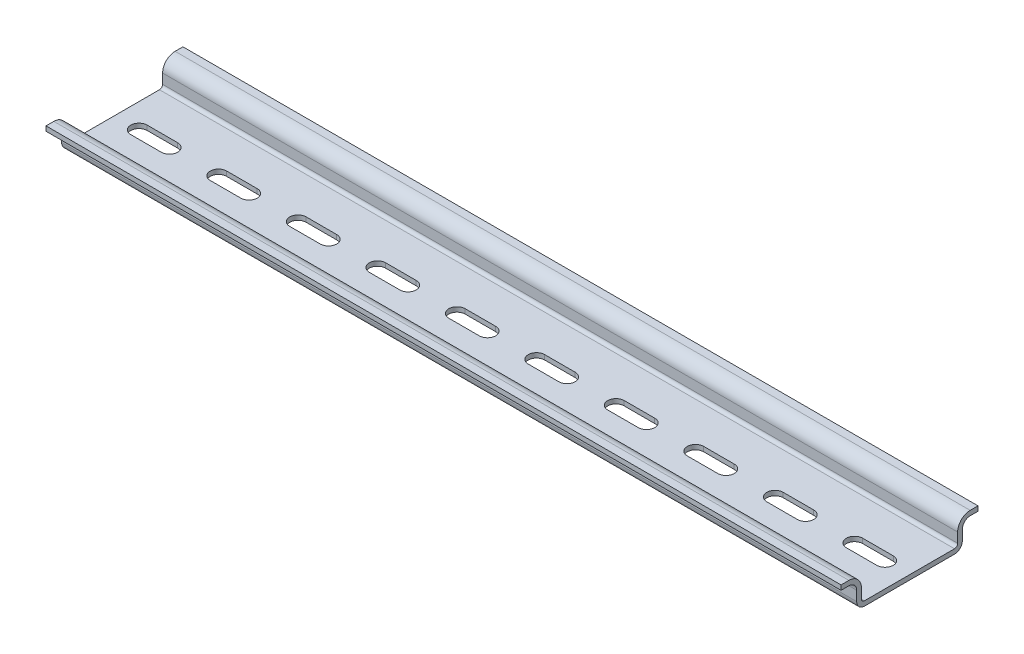
SolidWorks part; units mm, degrees
material "1060 Alloy"
ref_plane "Front Plane" through (0, 0, 0) normal (0, 0, 1) x (1, 0, 0)
ref_plane "Top Plane" through (0, 0, 0) normal (0, 1, 0) x (1, 0, 0)
ref_plane "Right Plane" through (0, 0, 0) normal (1, 0, 0) x (0, 0, -1)
sketch "Sketch1" plane through (0, 0, 0) normal (1, 0, 0) x (0, 0, -1)
  line L0 (0, 0) -> (0, 6.5) construction
  line L1 (0, 0) -> (17.5, 0) construction
  line L2 (-11.5, 0) -> (11.5, 0)
  line L3 (13.5, 2) -> (13.5, 4.5)
  line L4 (15.5, 6.5) -> (17.5, 6.5)
  line L5 (-13.5, 2) -> (-13.5, 4.5)
  line L6 (-15.5, 6.5) -> (-17.5, 6.5)
  arc A0 (13.5, 2) -> (11.5, 0) centre (11.5, 2) cw
  arc A1 (15.5, 6.5) -> (13.5, 4.5) centre (15.5, 4.5) ccw
  arc A2 (-13.5, 2) -> (-11.5, 0) centre (-11.5, 2) ccw
  arc A3 (-15.5, 6.5) -> (-13.5, 4.5) centre (-15.5, 4.5) cw
  point P9 (13.5, 0)
  dimension "D1" = 2
  dimension "D3" = 2
  dimension "D2" = 6.5
  dimension "D4" = 35
  dimension "D5" = 27
extrude "Extrude-Thin1" add sketch "Sketch1" along normal mid plane 203.2 thin thin type one direction wall 1.2
sketch "Sketch2" plane through (0, 0, 0) normal (0, -1, 0) x (1, 0, 0)
  line L0 (91.44, 2.1) -> (91.44, 0) construction
  line L1 (91.44, 0) -> (97.44, 0) construction
  line L2 (87.54, 2.1) -> (95.34, 2.1)
  line L3 (87.54, -2.1) -> (95.34, -2.1)
  line L4 (91.44, 0) -> (85.44, 0) construction
  line L5 (97.44, 0) -> (101.6, 0) construction
  line L6 (101.6, -11.5) -> (101.6, 11.5) construction
  arc A0 (95.34, 2.1) -> (95.34, -2.1) centre (95.34, 0) cw
  arc A1 (87.54, 2.1) -> (87.54, -2.1) centre (87.54, 0) ccw
  point P6 (91.44, 2.1)
  point P12 (91.44, -2.1)
  dimension "D2" = 12
  dimension "D1" = 4.2
  dimension "D3" = 4.16
extrude "Cut-Extrude1" cut sketch "Sketch2" against normal up to next (1.2 mm away)
pattern_linear "LPattern1" count 10 spacing 20.32 along (-1, 0, 0) of "Cut-Extrude1"
